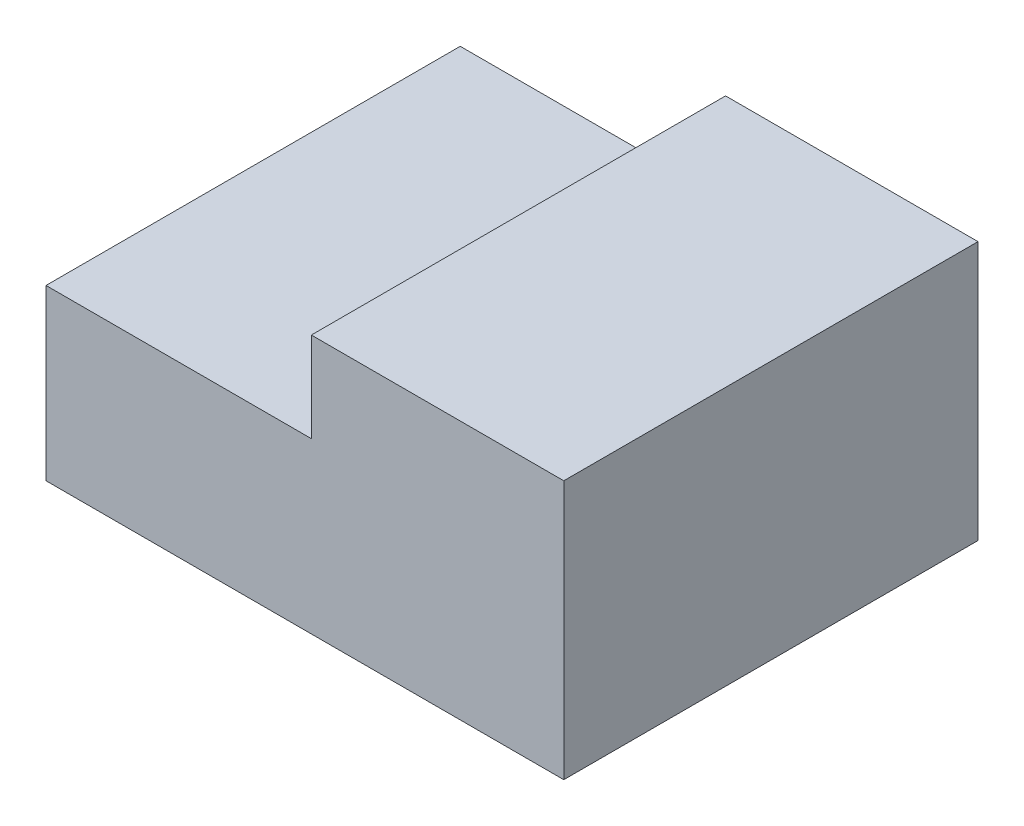
SolidWorks part; units mm, degrees
ref_plane "Alzado" through (0, 0, 0) normal (0, 0, 1) x (1, 0, 0)
ref_plane "Planta" through (0, 0, 0) normal (0, 1, 0) x (1, 0, 0)
ref_plane "Vista lateral" through (0, 0, 0) normal (1, 0, 0) x (0, 0, -1)
sketch "Croquis1" plane through (0, 0, 0) normal (0, 0, 1) x (1, 0, 0)
  line L1 (-108.0811, 75.7064) -> (-8.0811, 75.7064)
  line L2 (-108.0811, 75.7064) -> (-108.0811, 25.7064)
  line L3 (-108.0811, 25.7064) -> (-8.0811, 25.7064)
  line L4 (-8.0811, 75.7064) -> (-8.0811, 25.7064)
  line L5 (-108.0811, 75.7064) -> (-8.0811, 25.7064) construction
  line L6 (-108.0811, 25.7064) -> (-8.0811, 75.7064) construction
  dimension "D1" = 100
  dimension "D2" = 50
extrude "Saliente-Extruir1" add sketch "Croquis1" along normal blind 80
sketch "Croquis2" plane through (0, 0, 80) normal (0, 0, 1) x (1, 0, 0)
  line L0 (-108.0811, 58.3773) -> (-56.8332, 58.3773)
  line L1 (-108.0811, 75.7064) -> (-108.0811, 25.7064) construction
  line L2 (-56.8332, 58.3773) -> (-56.8332, 75.7064)
  line L3 (-8.0811, 75.7064) -> (-108.0811, 75.7064) construction
  line L4 (-56.8332, 75.7064) -> (-56.8332, 87.6662)
  line L5 (-56.8332, 87.6662) -> (-112.1811, 87.6662)
  line L6 (-112.1811, 87.6662) -> (-112.1811, 58.3773)
  line L7 (-112.1811, 58.3773) -> (-108.0811, 58.3773)
extrude "Cortar-Extruir1" cut sketch "Croquis2" against normal blind 100
